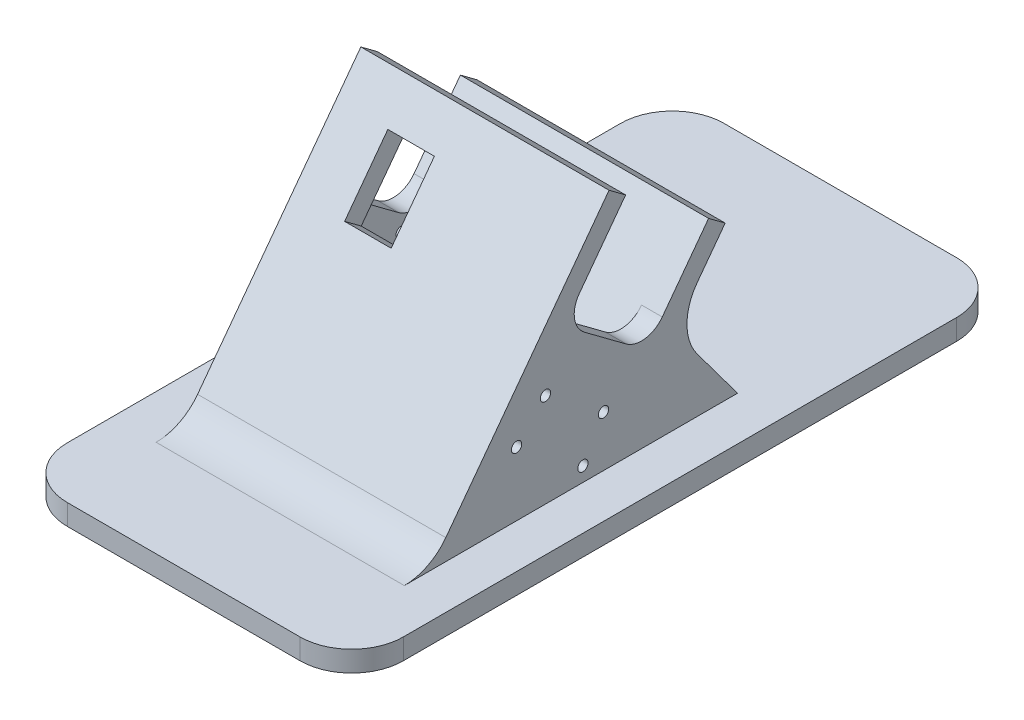
SolidWorks part; units mm, degrees
ref_plane "Front Plane" through (0, 0, 0) normal (0, 0, 1) x (1, 0, 0)
ref_plane "Top Plane" through (0, 0, 0) normal (0, 1, 0) x (1, 0, 0)
ref_plane "Right Plane" through (0, 0, 0) normal (1, 0, 0) x (0, 0, -1)
sketch "Sketch1" plane through (0, 0, 0) normal (0, 1, 0) x (1, 0, 0)
  line L1 (-22.5, -63.5) -> (22.5, -63.5)
  line L2 (-32.5, -53.5) -> (-32.5, 53.5)
  line L3 (-22.5, 63.5) -> (22.5, 63.5)
  line L4 (32.5, -53.5) -> (32.5, 53.5)
  line L5 (0, 63.5) -> (0, -63.5) construction
  line L6 (-32.5, 0) -> (32.5, 0) construction
  arc A0 (22.5, 63.5) -> (32.5, 53.5) centre (22.5, 53.5) cw
  arc A1 (22.5, -63.5) -> (32.5, -53.5) centre (22.5, -53.5) ccw
  arc A2 (-22.5, -63.5) -> (-32.5, -53.5) centre (-22.5, -53.5) cw
  arc A3 (-32.5, 53.5) -> (-22.5, 63.5) centre (-22.5, 53.5) cw
  point P0 (0, 0)
  dimension "D1" = 10
extrude "base_plate_extrude" add sketch "Sketch1" along normal blind 4
sketch "Sketch4" plane through (0, 4, 0) normal (0, 1, 0) x (1, 0, 0)
  line L1 (22.5, 63.5) -> (-22.5, 63.5) construction
  line L2 (0, 63.5) -> (0, -63.5) construction
  line L3 (-22.5, -63.5) -> (22.5, -63.5) construction
ref_plane "Plane1" through (0, 0, 0) normal (-1, 0, 0) x (0, 0, 1)
sketch "Sketch5" plane through (0, 0, 0) normal (-1, 0, 0) x (0, 0, 1)
  line L0 (-63.5, 4) -> (63.5, 4) construction
  line L1 (0, 4) -> (0, 34) construction
  line L2 (10, 4) -> (10, 34) construction
  line L3 (-10, 4) -> (-10, 34) construction
  line L4 (0, 34) -> (22.3431, 4) construction
  line L5 (-8.0201, 28.0269) -> (14.323, -1.9731) construction
  line L6 (8.0201, 39.9731) -> (30.3632, 9.9731) construction
  line L7 (22.3431, 4) -> (0, 4) construction
  line L8 (9.8744, 4) -> (25.9146, 15.9462) construction
  line L9 (25.9146, 15.9462) -> (9.8744, 4) construction
  line L10 (25.9146, 15.9462) -> (2.0221, 48.0266) construction
  line L11 (9.8744, 4) -> (-14.0181, 36.0804) construction
  line L12 (2.0221, 48.0266) -> (-14.0181, 36.0804) construction
  line L13 (31.5119, 15.1274) -> (2.8409, 53.6239)
  line L14 (2.8409, 53.6239) -> (-19.6154, 36.8992)
  line L15 (-11.8128, 26.4227) -> (-19.6154, 36.8992)
  line L16 (16.5711, 4) -> (31.5119, 15.1274) construction
  line L17 (36.8001, 8.0269) -> (31.5119, 15.1274)
  line L18 (-11.8128, 14.4765) -> (-19.6154, 4)
  line L19 (9.0556, -1.5973) -> (31.5119, 15.1274) construction
  line L20 (9.0556, -1.5973) -> (-19.6154, 36.8992) construction
  line L21 (39.7992, 4) -> (-19.6154, 4)
  line L22 (44.8202, 4) -> (53.5, 4) construction
  line L23 (44.8202, 4) -> (39.7992, 4)
  circle A0 centre (0, 34) radius 10 construction
  arc A1 (-11.8128, 14.4765) -> (-11.8128, 26.4227) centre (-19.8329, 20.4496) ccw
  arc A2 (36.8001, 8.0269) -> (44.8202, 4) centre (44.8202, 14) ccw
  spline S0 degree 1 poles (31.5119, 15.1274) (34.156, 11.5772) knots 0 0 1 1
  spline S1 degree 1 poles (-19.6154, 36.8992) (-7.3642, 20.4496) knots 0 0 1 1 construction
  dimension "D5" = 4
  dimension "D6" = 10
  dimension "D7" = 10
  dimension "D3" = 10
  dimension "D1" = 10
  dimension "D2" = 10
  dimension "D4" = 10
extrude "MotorCaseExtrude" add sketch "Sketch5" along normal blind 24 and the other way blind 24 contours L17 A2 L23 L21 L18 A1 L15 L14 L13
sketch "Sketch7" plane through (0, 33.131, -24.6749) normal (0, 0.802, -0.5973) x (1, 0, 0)
  line L0 (24, -6.3086) -> (-24, -34.3086) construction
  line L1 (-24, -6.3086) -> (24, -34.3086) construction
  line L7 (-20, -30.3086) -> (20, -30.3086)
  line L8 (-20, -30.3086) -> (-20, -10.3086)
  line L9 (-20, -10.3086) -> (20, -10.3086)
  line L10 (20, -30.3086) -> (20, -10.3086)
  line L11 (0, -10.3086) -> (0, -30.3086) construction
  line L12 (-20, -20.3086) -> (20, -20.3086) construction
  point P8 (0, -20.3086)
  point P9 (0, -20.3086)
extrude "Cut-Extrude1" cut sketch "Sketch7" against normal blind 44
sketch "Sketch9" plane through (0, 20.4929, 27.5158) normal (0, 0.5973, 0.802) x (1, 0, 0)
  line L0 (24, -15.5435) -> (24, 41.3099) construction
  line L1 (-24, 41.3099) -> (24, 41.3099)
  line L2 (-24, 41.3099) -> (-24, 37.3099)
  line L3 (-24, 37.3099) -> (24, 37.3099)
  line L4 (24, 41.3099) -> (24, 37.3099)
extrude "Cut-Extrude2" cut sketch "Sketch9" against normal blind 28
sketch "Sketch10" plane through (-24, 0, 0) normal (-1, 0, 0) x (0, 0, 1)
  line L0 (5.2301, 50.4158) -> (2.0221, 48.0266) construction
  line L1 (-17.2261, 33.6911) -> (-14.0181, 36.0804) construction
  line L6 (-14.0181, 36.0804) -> (2.0221, 48.0266)
  line L7 (-14.0181, 36.0804) -> (-5.0584, 24.0502)
  line L8 (2.0221, 48.0266) -> (10.9818, 35.9965)
  line L9 (1.9382, 23.0267) -> (9.9583, 28.9999)
  arc A2 (9.9583, 28.9999) -> (10.9818, 35.9965) centre (6.9717, 33.0099) ccw
  arc A3 (1.9382, 23.0267) -> (-5.0584, 24.0502) centre (-1.0484, 27.0368) cw
  dimension "D1" = 5
  dimension "D2" = 5
extrude "fillet" cut sketch "Sketch10" against normal blind 48
sketch "Sketch11" plane through (0, 20.4929, 27.5158) normal (0, 0.5973, 0.802) x (1, 0, 0)
  line L0 (-24, 37.3099) -> (-24, 29.3099) construction
  line L1 (-24, -15.5435) -> (-24, 37.3099) construction
  line L2 (-24, 29.3099) -> (-14, 29.3099) construction
  line L3 (-24, 37.3099) -> (-24, 15.3099) construction
  line L4 (-24, 15.3099) -> (-5, 15.3099) construction
  line L10 (-14, 29.3099) -> (-5, 29.3099)
  line L11 (-14, 29.3099) -> (-14, 15.3099)
  line L12 (-14, 15.3099) -> (-5, 15.3099)
  line L13 (-5, 29.3099) -> (-5, 15.3099)
extrude "Hole for wire" cut sketch "Sketch11" against normal blind 4
sketch "Sketch13" plane through (-20, 0, 0) normal (1, 0, 0) x (0, 0, -1)
  circle A2 centre (-6.3068, 13.8116) radius 1
  circle A4 centre (-1.4259, 19.528) radius 1
  circle A6 centre (-13.456, 28.4877) radius 1
  circle A8 centre (-17.5349, 22.174) radius 1
extrude "Cut-Extrude3" cut sketch "Sketch13" against normal up to next
sketch "Sketch14" plane through (20, 0, 0) normal (-1, 0, 0) x (0, 0, 1)
  circle A2 centre (10.2838, 6.7986) radius 1
  circle A4 centre (23.1159, 16.3556) radius 1
  circle A6 centre (6.3073, 13.812) radius 1
  circle A8 centre (17.5354, 22.1744) radius 1
extrude "Cut-Extrude4" cut sketch "Sketch14" against normal up to next
sketch "Sketch12" plane through (0, 29.9229, -22.2857) normal (0, 0.802, -0.5973) x (1, 0, 0)
  line L0 (-24, -6.3086) -> (24, -6.3086) construction
  line L1 (-24, -34.3086) -> (-20, -34.3086)
  line L2 (-24, -34.3086) -> (-24, -6.3086)
  line L3 (-24, -6.3086) -> (-20, -6.3086)
  line L4 (-20, -34.3086) -> (-20, -6.3086)
  line L6 (24, -34.3086) -> (20, -34.3086)
  line L7 (24, -34.3086) -> (24, -6.3086)
  line L8 (24, -6.3086) -> (20, -6.3086)
  line L9 (20, -34.3086) -> (20, -6.3086)
ref_plane "Plane2" through (0, 0, 0) normal (-1, 0, 0) x (0, 0, 1)
